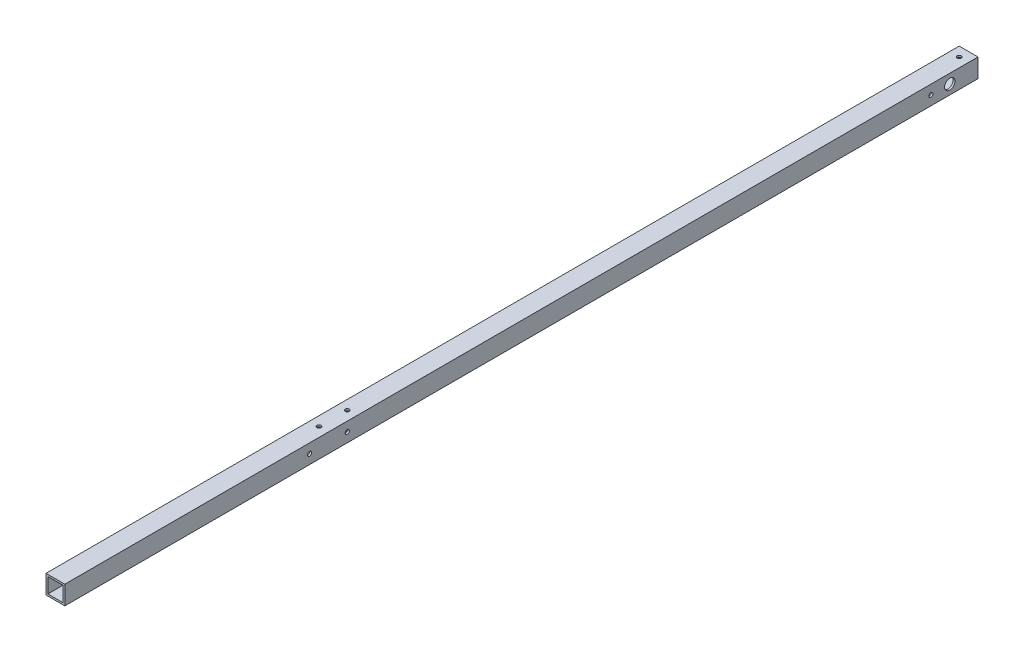
SolidWorks part; units mm, degrees
ref_plane "正面" through (0, 0, 0) normal (0, 0, 1) x (1, 0, 0)
ref_plane "平面" through (0, 0, 0) normal (0, 1, 0) x (1, 0, 0)
ref_plane "右側面" through (0, 0, 0) normal (1, 0, 0) x (0, 0, -1)
sketch "ｽｹｯﾁ1" plane through (0, 0, 0) normal (0, 0, 1) x (1, 0, 0)
  line L1 (-10, 10) -> (10, 10)
  line L2 (-10, 10) -> (-10, -10)
  line L3 (-10, -10) -> (10, -10)
  line L4 (10, 10) -> (10, -10)
  line L5 (-10, 10) -> (10, -10) construction
  line L6 (-10, -10) -> (10, 10) construction
  line L7 (-8, 8) -> (8, 8)
  line L8 (-8, 8) -> (-8, -8)
  line L9 (-8, -8) -> (8, -8)
  line L10 (8, 8) -> (8, -8)
  line L11 (-8, 8) -> (8, -8) construction
  line L12 (-8, -8) -> (8, 8) construction
  point P0 (0, 0)
  point P6 (0, 0)
  dimension "D1" = 20
  dimension "D2" = 20
  dimension "D3" = 16
  dimension "D4" = 16
extrude "ﾎﾞｽ - 押し出し1" add sketch "ｽｹｯﾁ1" along normal blind 970
sketch "ｽｹｯﾁ2" plane through (10, 0, 0) normal (1, 0, 0) x (0, 0, -1)
  line L0 (-970, 0) -> (-710, 0)
  line L1 (-970, -10) -> (-970, 10) construction
  line L2 (-710, 0) -> (-890.4665, 0)
  line L3 (-890.4665, 0) -> (-845.8821, 0)
  line L4 (-845.8821, 0) -> (-803.5394, 0)
  line L5 (-710, 0) -> (-670, 0)
  line L6 (-670, 0) -> (-50, 0)
  line L7 (-50, 0) -> (-30, 0)
  circle A0 centre (-710, 0) radius 2.2
  circle A4 centre (-670, 0) radius 2.2
  circle A5 centre (-50, 0) radius 2.2
  circle A6 centre (-30, 0) radius 5.5
  dimension "D5" = 11
  dimension "D6" = 4.4
  dimension "D7" = 4.4
  dimension "D8" = 4.4
  dimension "D1" = 260
  dimension "D2" = 40
  dimension "D3" = 620
  dimension "D4" = 20
extrude "ｶｯﾄ - 押し出し1" cut sketch "ｽｹｯﾁ2" against normal blind 970
sketch "ｽｹｯﾁ3" plane through (0, 10, 0) normal (0, 1, 0) x (1, 0, 0)
  line L0 (0, -970) -> (0, -690)
  line L1 (10, -970) -> (-10, -970) construction
  line L2 (0, -690) -> (0, -660)
  line L3 (0, -660) -> (0, -10)
  circle A0 centre (0, -690) radius 2.2
  circle A1 centre (0, -660) radius 2.2
  circle A2 centre (0, -10) radius 2.2
  dimension "D2" = 4.4
  dimension "D4" = 4.4
  dimension "D6" = 4.4
  dimension "D1" = 280
  dimension "D3" = 30
  dimension "D5" = 650
extrude "ｶｯﾄ - 押し出し2" cut sketch "ｽｹｯﾁ3" against normal blind 970
